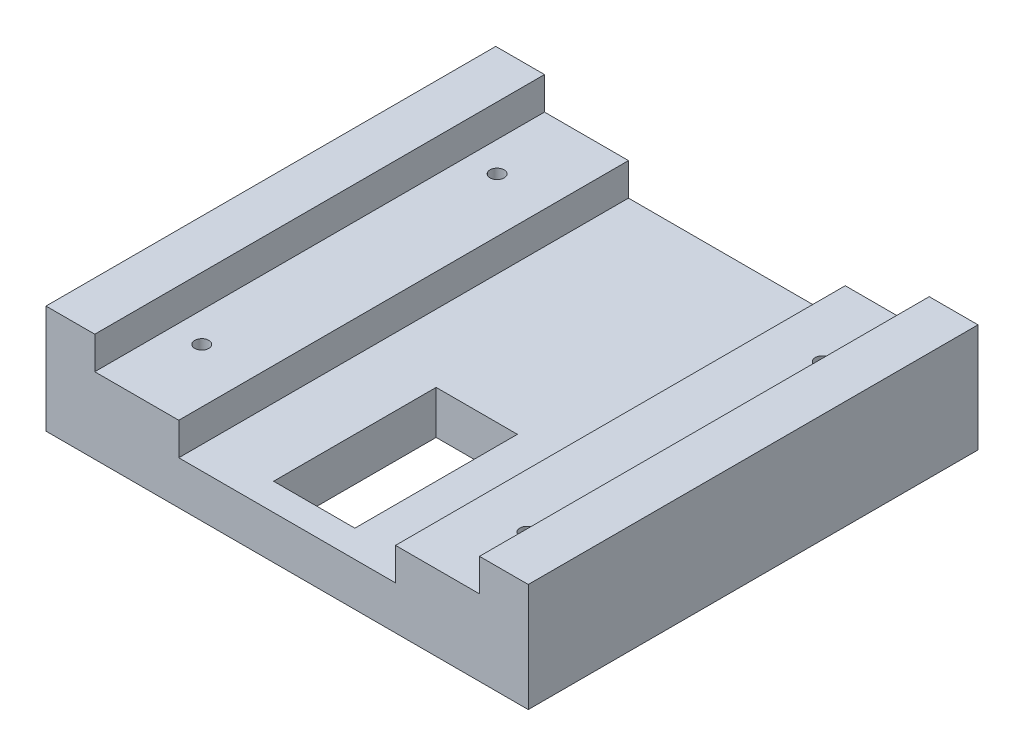
SolidWorks part; units mm, degrees
ref_plane "Front Plane" through (0, 0, 0) normal (0, 0, 1) x (1, 0, 0)
ref_plane "Top Plane" through (0, 0, 0) normal (0, 1, 0) x (1, 0, 0)
ref_plane "Right Plane" through (0, 0, 0) normal (1, 0, 0) x (0, 0, -1)
sketch "Sketch1" plane through (0, 0, 0) normal (0, 1, 0) x (1, 0, 0)
  line L9 (-44.5, 0) -> (44.5, 0)
  line L10 (-44.5, 0) -> (-44.5, 83)
  line L11 (-44.5, 83) -> (44.5, 83)
  line L12 (44.5, 0) -> (44.5, 83)
  line L13 (34.5, 0) -> (-34.5, 0) construction
  line L14 (34.5, 0) -> (34.5, 83) construction
  line L15 (34.5, 83) -> (-34.5, 83) construction
  line L16 (-34.5, 0) -> (-34.5, 83) construction
  line L17 (-7.5, 5) -> (7.5, 5)
  line L18 (-7.5, 5) -> (-7.5, 35)
  line L19 (-7.5, 35) -> (7.5, 35)
  line L20 (7.5, 5) -> (7.5, 35)
  line L21 (-30, 14.25) -> (30, 14.25) construction
  line L22 (-30, 14.25) -> (-30, 68.75) construction
  line L23 (-30, 68.75) -> (30, 68.75) construction
  line L24 (30, 14.25) -> (30, 68.75) construction
  circle A0 centre (30, 14.25) radius 1.3
  circle A1 centre (-30, 14.25) radius 1.3
  circle A2 centre (-30, 68.75) radius 1.3
  circle A3 centre (30, 68.75) radius 1.3
  circle A4 centre (-30, 68.75) radius 1.75 construction
  point P9 (0, 0)
  point P10 (0, 0)
  point P16 (0, 5)
  point P25 (0, 14.25)
  point P27 (44.5, 41.5)
  point P28 (30, 41.5)
  dimension "D7" = 2.6
  dimension "D8" = 3.5
  dimension "D1" = 83
  dimension "D2" = 69
  dimension "D3" = 10
  dimension "D4" = 15
  dimension "D5" = 30
  dimension "D6" = 5
  dimension "D9" = 60
  dimension "D10" = 54.5
extrude "Main Body" add sketch "Sketch1" along normal blind 14 contours L9 L12 L11 L10 A3 A2 A1 A0 L20 L17 L18 L19
sketch "Sketch2" plane through (0, 14, 0) normal (0, 1, 0) x (1, 0, 0)
  line L1 (-20, 0) -> (20, 0)
  line L2 (-20, 0) -> (-20, 83)
  line L3 (-20, 83) -> (20, 83)
  line L4 (20, 0) -> (20, 83)
  line L7 (-44.5, 83) -> (44.5, 83) construction
  point P4 (-20, 0)
  point P5 (20, 79.8433)
  point P6 (20, 83)
  point P8 (0, 0)
  dimension "D1" = 40
extrude "Screw Groove" cut sketch "Sketch2" against normal blind 6
sketch "Sketch4" plane through (0, 14, 0) normal (0, 1, 0) x (1, 0, 0)
  line L0 (-44.5, 0) -> (-20, 0) construction
  line L1 (-44.5, 83) -> (-35.5, 83)
  line L2 (-44.5, 83) -> (-44.5, 0)
  line L3 (-44.5, 0) -> (-35.5, 0)
  line L4 (-35.5, 83) -> (-35.5, 0)
  line L5 (20, 83) -> (44.5, 83) construction
  line L6 (44.5, 0) -> (35.5, 0)
  line L7 (44.5, 0) -> (44.5, 83)
  line L8 (44.5, 83) -> (35.5, 83)
  line L9 (35.5, 0) -> (35.5, 83)
  dimension "D1" = 71
extrude "Boss-Extrude2" add sketch "Sketch4" along normal blind 6
